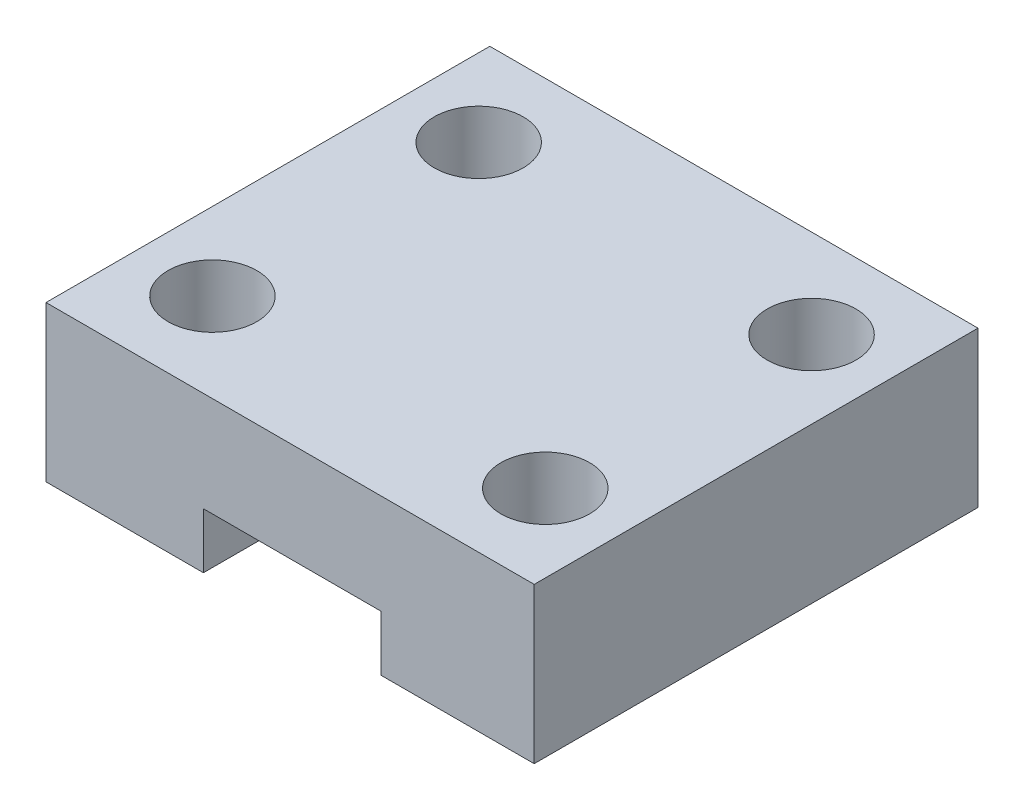
SolidWorks part; units mm, degrees
material "Ductile Iron (SN)"
ref_plane "Front Plane" through (0, 0, 0) normal (0, 0, 1) x (1, 0, 0)
ref_plane "Top Plane" through (0, 0, 0) normal (0, 1, 0) x (1, 0, 0)
ref_plane "Right Plane" through (0, 0, 0) normal (1, 0, 0) x (0, 0, -1)
sketch "Sketch1" plane through (0, 0, 0) normal (0, 1, 0) x (1, 0, 0)
  line L1 (-22.1889, 23.5576) -> (21.8111, 23.5576)
  line L2 (-22.1889, 23.5576) -> (-22.1889, -16.4424)
  line L3 (-22.1889, -16.4424) -> (21.8111, -16.4424)
  line L4 (21.8111, 23.5576) -> (21.8111, -16.4424)
  circle A0 centre (14.8111, -8.4424) radius 4
  circle A1 centre (14.8111, 15.5576) radius 4
  circle A2 centre (-15.1889, 15.5576) radius 4
  circle A3 centre (-15.1889, -8.4424) radius 4
  point P0 (0, 0)
  dimension "D3" = 7
  dimension "D4" = 8
  dimension "D5" = 7
  dimension "D1" = 40
  dimension "D2" = 44
  dimension "D6" = 8
  dimension "D7" = 8
extrude "Boss-Extrude1" add sketch "Sketch1" along normal blind 14
sketch "Sketch2" plane through (0, 0, 0) normal (0, 0, 1) x (1, 0, 0)
  line L1 (-8, 5) -> (8, 5)
  line L2 (-8, 5) -> (-8, -2.1149)
  line L3 (-8, -2.1149) -> (8, -2.1149)
  line L4 (8, 5) -> (8, -2.1149)
  line L5 (-8, 5) -> (8, -2.1149) construction
  line L6 (-8, -2.1149) -> (8, 5) construction
  point P0 (0, 1.4425)
  dimension "D2" = 16
  dimension "D1" = 5
extrude "Cut-Extrude1" cut sketch "Sketch2" along normal up to surface and the other way up to surface up to face at (-0.1889, 7, 16.4424) other way up to face at (-0.1889, 7, -23.5576)
